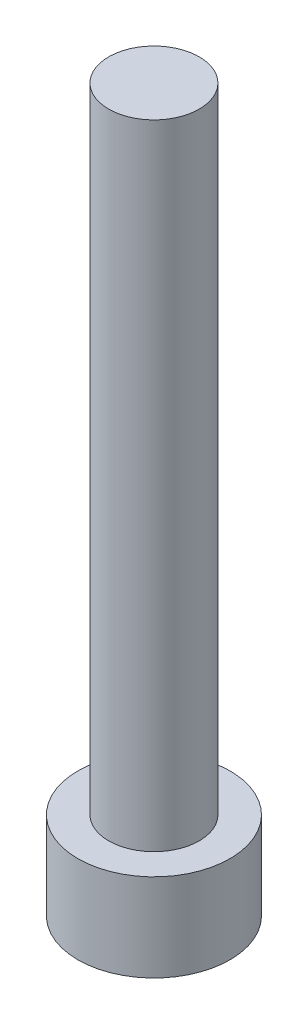
SolidWorks part; units mm, degrees
ref_plane "前视基准面" through (0, 0, 0) normal (0, 0, 1) x (1, 0, 0)
ref_plane "上视基准面" through (0, 0, 0) normal (0, 1, 0) x (1, 0, 0)
ref_plane "右视基准面" through (0, 0, 0) normal (1, 0, 0) x (0, 0, -1)
sketch "草图1" plane through (0, 0, 0) normal (0, 1, 0) x (1, 0, 0)
  circle A0 centre (0, 0) radius 4.2
extrude "凸台-拉伸1" add sketch "草图1" along normal blind 4.84
sketch "草图2" plane through (0, 4.84, 0) normal (0, 1, 0) x (1, 0, 0)
  circle A0 centre (0, 0) radius 2.5
extrude "凸台-拉伸2" add sketch "草图2" along normal blind 35
sketch "草图3" plane through (0, 0, 0) normal (0, -1, 0) x (1, 0, 0)
  line L1 (2.3, 0) -> (1.15, 1.9919)
  line L2 (1.15, 1.9919) -> (-1.15, 1.9919)
  line L3 (-1.15, 1.9919) -> (-2.3, 0)
  line L4 (-2.3, 0) -> (-1.15, -1.9919)
  line L5 (-1.15, -1.9919) -> (1.15, -1.9919)
  line L6 (1.15, -1.9919) -> (2.3, 0)
  circle A0 centre (0, 0) radius 1.9919 construction
extrude "切除-拉伸1" cut sketch "草图3" against normal blind 3.4
